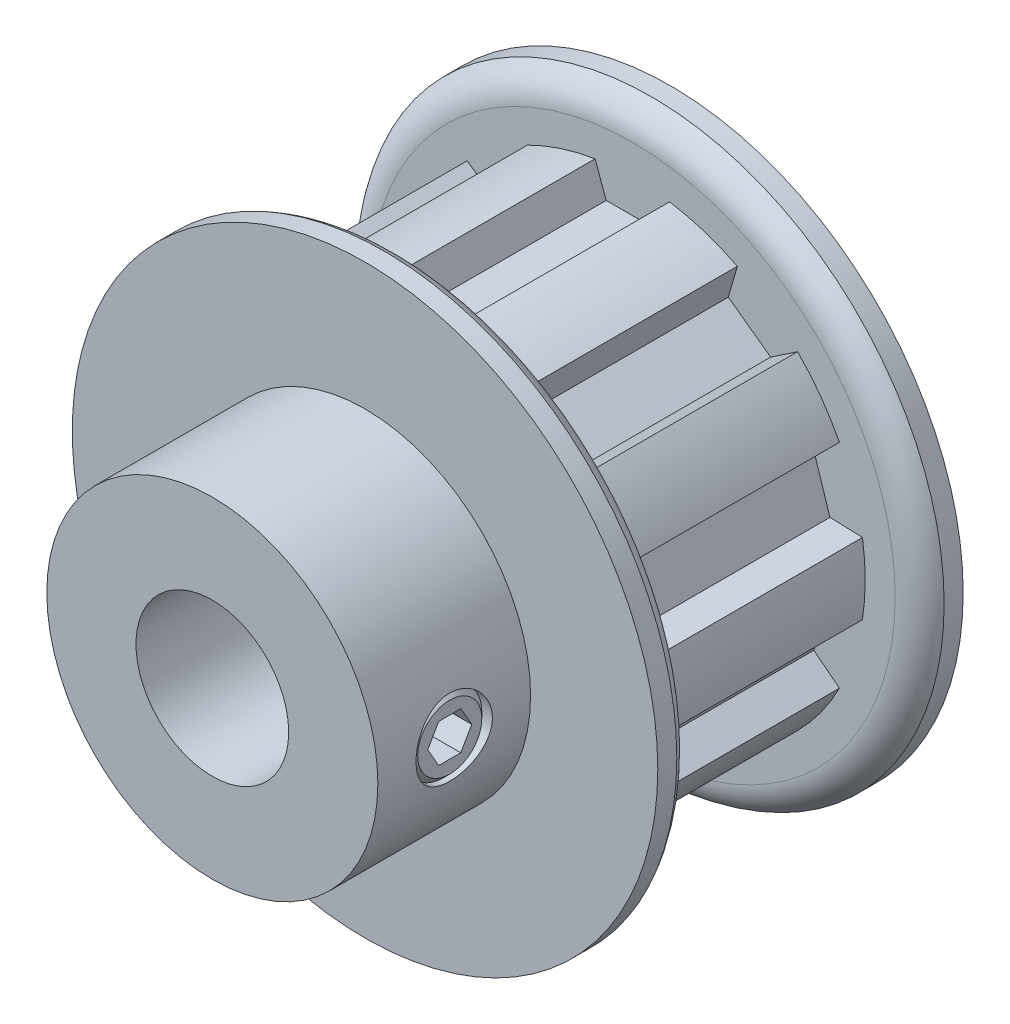
SolidWorks part; units mm, degrees
ref_plane "Front Plane" through (0, 0, 0) normal (0, 0, 1) x (1, 0, 0)
ref_plane "Top Plane" through (0, 0, 0) normal (0, 1, 0) x (1, 0, 0)
ref_plane "Right Plane" through (0, 0, 0) normal (1, 0, 0) x (0, 0, -1)
sketch "Sketch1" plane through (0, 0, 0) normal (0, 0, 1) x (1, 0, 0)
  line L0 (-2.3241, 14.3383) -> (-1.6307, 12.4333)
  line L1 (-1.6307, 12.4333) -> (1.6307, 12.4333)
  line L2 (1.6307, 12.4333) -> (2.3241, 14.3383)
  line L3 (-2.3241, 14.3383) -> (2.3241, 14.3383)
  line L4 (0, 0) -> (0, 12.4333) construction
  line L5 (0, 12.4333) -> (0, 15.9893) construction
  circle A0 centre (0, 0) radius 15.1638 construction
  circle A1 centre (0, 0) radius 18.2626 construction
  circle A2 centre (0, 0) radius 14.5254 construction
  point P6 (0, 14.3383)
  point P11 (0, 15.1638)
  point P13 (0, 18.2626)
  point P14 (0, 14.5254)
  dimension "D1" = 1.651
  dimension "D2" = 0.8255
sketch "Sketch2" plane through (0, 0, 0) normal (1, 0, 0) x (0, 0, -1)
  line L0 (-14.2875, 4.7625) -> (14.2875, 4.7625)
  line L1 (-14.2875, 4.7625) -> (-14.2875, 10.3251)
  line L2 (-14.2875, 10.3251) -> (-4.7625, 10.3251)
  line L3 (-4.7625, 10.3251) -> (-4.7625, 18.2626)
  line L4 (-4.7625, 18.2626) -> (-2.3876, 18.2626) construction
  line L5 (-2.3876, 18.2626) -> (-2.3876, 14.5254) construction
  line L6 (-2.3876, 14.5254) -> (11.9126, 14.5254)
  line L7 (11.9126, 14.5254) -> (11.9126, 18.2626) construction
  line L8 (11.9126, 18.2626) -> (14.2875, 18.2626) construction
  line L9 (14.2875, 18.2626) -> (14.2875, 4.7625)
  line L10 (-14.2875, 0) -> (14.2875, 0) construction
  line L13 (-4.7625, 18.2626) -> (-3.5751, 18.2626)
  line L14 (-2.3876, 16.394) -> (-2.3876, 14.5254)
  line L15 (11.9126, 14.5254) -> (11.9126, 16.394)
  line L16 (13.1, 18.2626) -> (14.2875, 18.2626)
  arc A0 (-2.3876, 16.394) -> (-3.5751, 18.2626) centre (-4.4515, 16.394) ccw
  arc A1 (11.9126, 16.394) -> (13.1, 18.2626) centre (13.9765, 16.394) cw
  point P12 (-2.3876, 16.394)
  point P14 (-3.5751, 18.2626)
  point P20 (11.9126, 16.394)
  point P21 (13.1, 18.2626)
  point P25 (11.9126, 0)
  point P26 (-2.3876, 0)
  dimension "Bore" = 9.525
  dimension "Hub Dia" = 20.6502
  dimension "Outside Width" = 19.05
  dimension "Inside Width" = 14.3002
revolve "Revolve1" add sketch "Sketch2" angle 360 mid plane about L10
sketch "Sketch3" plane through (0, 0, 0) normal (0, 0, 1) x (1, 0, 0)
  line L0 (-1.6307, 12.4333) -> (1.6307, 12.4333) construction
  line L1 (1.6307, 12.4333) -> (2.3241, 14.3383) construction
  line L2 (-2.3241, 14.3383) -> (-1.6307, 12.4333) construction
  line L3 (-1.6307, 12.4333) -> (1.6307, 12.4333)
  line L4 (1.6307, 12.4333) -> (2.3241, 14.3383)
  line L5 (-2.3241, 14.3383) -> (-1.6307, 12.4333)
  circle A0 centre (0, 0) radius 14.5254 construction
  arc A1 (2.3241, 14.3383) -> (-2.3241, 14.3383) centre (0, 0) ccw
extrude "Cut-Extrude1" cut sketch "Sketch3" against normal up to vertex (11.9126 mm away) from vertex at 2.3876 starting at point (0, 14.5254, 2.3876)
pattern_circular "CirPattern1" count 10 over 360 about axis through (0, 0, 0) along (0, 0, 1) of "Cut-Extrude1"
sketch "Sketch4" plane through (0, 0, 0) normal (1, 0, 0) x (0, -1, 0)
  line L0 (0, -4.7625) -> (0, -14.2875) construction
  line L1 (-10.3251, -4.7625) -> (10.3251, -4.7625) construction
  line L2 (-10.3251, -14.2875) -> (10.3251, -14.2875) construction
  circle A0 centre (0, -9.525) radius 2.3813
  dimension "D1" = 4.7625
extrude "Cut-Extrude2" cut sketch "Sketch4" along normal through all
ref_plane "Plane1" through (0, 0, 9.525) normal (0, 0, 1) x (1, 0, 0)
sketch "Sketch5" plane through (0, 0, 9.525) normal (0, 0, 1) x (1, 0, 0)
  line L0 (0, 0.1664) -> (0, 10.3251) construction
  line L1 (4.7625, -2.0003) -> (4.7625, 0)
  line L2 (5.1435, -2.3813) -> (9.6658, -2.3813)
  line L3 (4.7625, 0) -> (10.3251, 0) construction
  line L4 (4.7625, 0) -> (10.0468, 0)
  line L5 (10.0468, 0) -> (10.0468, -2.0003)
  line L6 (5.1435, -2.3813) -> (4.7625, -2.0003)
  line L7 (10.0468, -2.0003) -> (9.6658, -2.3813)
  circle A0 centre (0, 0) radius 10.3251 construction
  circle A1 centre (0, 0) radius 4.7625 construction
  point P2 (4.7625, -2.3813)
  point P11 (10.0468, -2.3813)
revolve "Revolve2" add sketch "Sketch5" angle 360 mid plane about L4
sketch "Sketch6" plane through (10.0468, 5.3841, 0) normal (-1, 0, 0) x (0, -1, 0)
  line L1 (5.3841, 10.8998) -> (4.1935, 10.2124)
  line L2 (4.1935, 10.2124) -> (4.1935, 8.8376)
  line L3 (4.1935, 8.8376) -> (5.3841, 8.1502)
  line L4 (5.3841, 8.1502) -> (6.5748, 8.8376)
  line L5 (6.5748, 8.8376) -> (6.5748, 10.2124)
  line L6 (6.5748, 10.2124) -> (5.3841, 10.8998)
  circle A0 centre (5.3841, 9.525) radius 1.1906 construction
  dimension "D1" = 2.3813
extrude "Cut-Extrude3" cut sketch "Sketch6" along normal blind 1.7859
equation "\"D2@Sketch1\" = \"D1@Sketch1\"/2"
equation "\"D1@Sketch4\" = \"Bore@Sketch2\"/2"
equation "\"D1@Sketch6\" = \"D1@Sketch4\"/2"
equation "\"D1@Cut-Extrude3\" = \"D1@Sketch6\"*.75"
